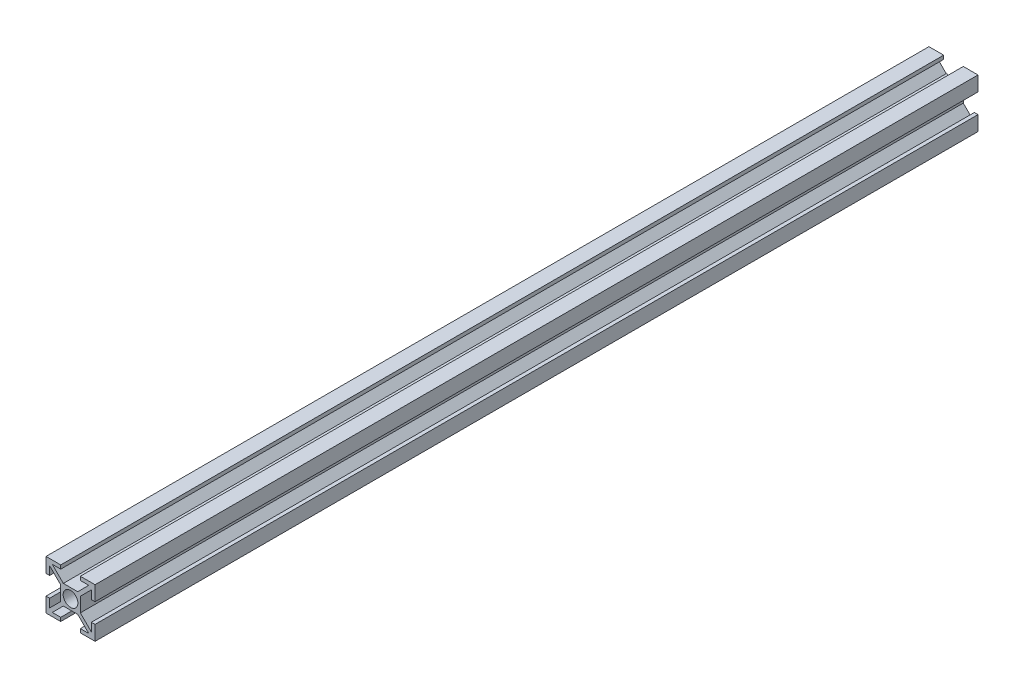
SolidWorks part; units mm, degrees
material "3.0205 (EN-AW 1200)"
ref_plane "Plano frontal" through (0, 0, 0) normal (0, 0, 1) x (1, 0, 0)
ref_plane "Plano superior" through (0, 0, 0) normal (0, 1, 0) x (1, 0, 0)
ref_plane "Plano direito" through (0, 0, 0) normal (1, 0, 0) x (0, 0, -1)
sketch "Esboço1" plane through (0, 0, 0) normal (0, 0, 1) x (1, 0, 0)
  line L0 (-2.9393, 4) -> (2.9393, 4)
  line L1 (-10, -10) -> (-4, -10)
  line L2 (-10, -10) -> (-10, -4)
  line L3 (-10, 10) -> (-4, 10)
  line L4 (10, -10) -> (10, -4)
  line L5 (-10, -10) -> (-4, -4) construction
  line L6 (-10, 10) -> (-4, 4) construction
  line L7 (-7.4393, -8.5) -> (-2.9393, -4)
  line L8 (4, -10) -> (10, -10)
  line L9 (-8.5, -7.4393) -> (-4, -2.9393)
  line L10 (-8.5, 7.4393) -> (-4, 2.9393)
  line L11 (-7.4393, -8.5) -> (-4, -8.5)
  line L12 (-8.5, -7.4393) -> (-8.5, -4)
  line L13 (-7.4393, 8.5) -> (-4, 8.5)
  line L14 (8.5, -7.4393) -> (8.5, -4)
  line L15 (-8.5, -8.5) -> (-4, -4) construction
  line L16 (-8.5, 8.5) -> (-4, 4) construction
  line L17 (-4, 10) -> (-4, 8.5)
  line L18 (4, -8.5) -> (7.4393, -8.5)
  line L19 (-10, -4) -> (-8.5, -4)
  line L20 (4, 10) -> (4, 8.5)
  line L21 (-10, 4) -> (-8.5, 4)
  line L22 (-4, 2.9393) -> (-4, -2.9393)
  line L23 (-4, -8.5) -> (-4, -10)
  line L24 (-8.5, 4) -> (-8.5, 7.4393)
  line L25 (-10, 4) -> (-10, 10)
  line L26 (-7.4393, 8.5) -> (-2.9393, 4)
  line L27 (4, 8.5) -> (7.4393, 8.5)
  line L28 (-2.9393, -4) -> (2.9393, -4)
  line L29 (4, 10) -> (10, 10)
  line L30 (4, -8.5) -> (4, -10)
  line L31 (10, 4) -> (10, 10)
  line L32 (8.5, 4) -> (8.5, 7.4393)
  line L33 (-10.5303, -9.4697) -> (9.4697, 10.5303) construction
  line L34 (8.5, 4) -> (10, 4)
  line L35 (8.5, -4) -> (10, -4)
  line L36 (-10, -10) -> (10, 10) construction
  line L37 (4, 2.9393) -> (4, -2.9393)
  line L38 (-9.4697, -10.5303) -> (10.5303, 9.4697) construction
  line L40 (2.9393, -4) -> (7.4393, -8.5)
  line L41 (4, -4) -> (10, -10) construction
  line L42 (4, -4) -> (8.5, -8.5) construction
  line L43 (4, -2.9393) -> (8.5, -7.4393)
  line L44 (4, 0) -> (10, 0) construction
  line L45 (4, 2.9393) -> (8.5, 7.4393)
  line L46 (4, 4) -> (8.5, 8.5) construction
  line L47 (4, 4) -> (10, 10) construction
  line L48 (2.9393, 4) -> (7.4393, 8.5)
  circle A0 centre (0, 0) radius 3
  point P0 (0, 0)
  point P14 (0, 0)
  dimension "D1" = 0.75
  dimension "D3" = 1.5
  dimension "D4" = 20
  dimension "D2" = 0.75
extrude "Ressalto-extrusão1" add sketch "Esboço1" along normal blind 360
